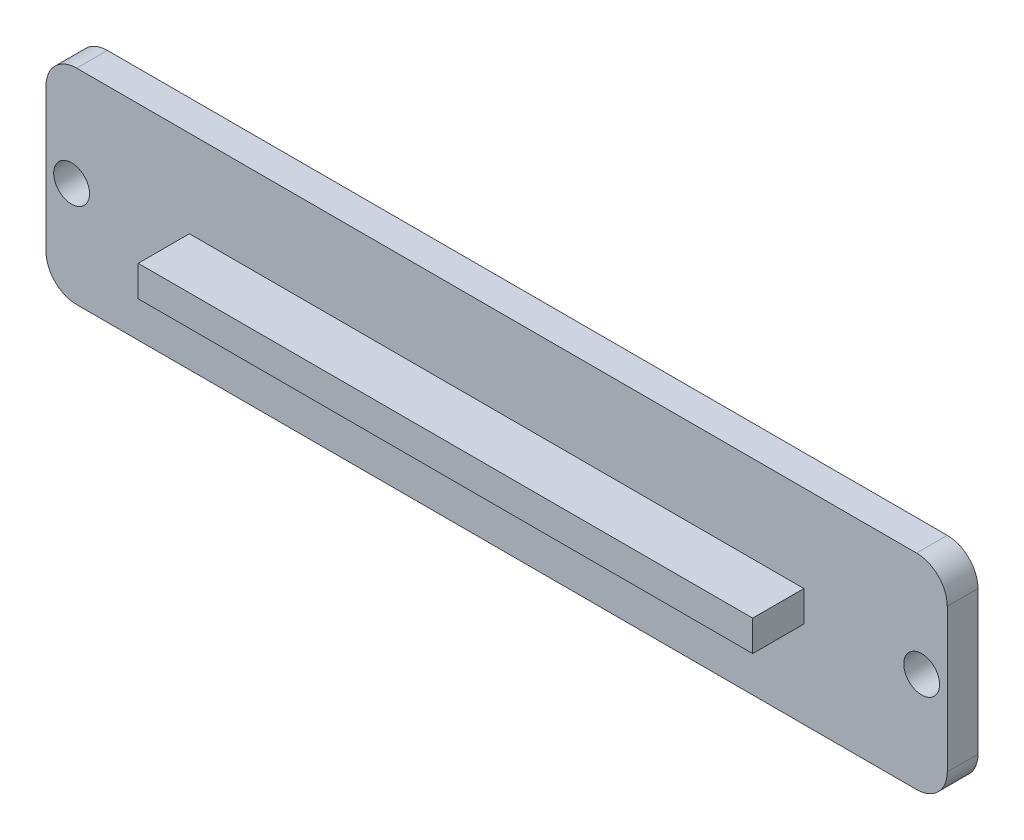
SolidWorks part; units mm, degrees
ref_plane "Plan de face" through (0, 0, 0) normal (0, 0, 1) x (1, 0, 0)
ref_plane "Plan de dessus" through (0, 0, 0) normal (0, 1, 0) x (1, 0, 0)
ref_plane "Plan de droite" through (0, 0, 0) normal (1, 0, 0) x (0, 0, -1)
sketch "Esquisse1" plane through (0, 0, 0) normal (0, 0, 1) x (1, 0, 0)
  line L0 (2.5, 10) -> (85.5, 10) construction
  line L1 (0, 0) -> (88, 0)
  line L2 (0, 0) -> (0, 20)
  line L3 (0, 20) -> (88, 20)
  line L4 (88, 0) -> (88, 20)
  circle A0 centre (2.5, 10) radius 1.75
  circle A1 centre (85.5, 10) radius 1.75
  point P9 (0, 10)
  point P10 (44, 10)
  point P11 (44, 20)
  dimension "D3" = 3.5
  dimension "D1" = 20
  dimension "D2" = 88
  dimension "D4" = 83
extrude "Boss.-Extru.1" add sketch "Esquisse1" along normal blind 3
sketch "Esquisse2" plane through (0, 0, 3) normal (0, 0, 1) x (1, 0, 0)
  line L0 (0, 20) -> (0, 0) construction
  line L1 (14, 11.5) -> (74, 11.5)
  line L2 (14, 11.5) -> (14, 8.5)
  line L3 (14, 8.5) -> (74, 8.5)
  line L4 (74, 11.5) -> (74, 8.5)
  line L5 (88, 20) -> (0, 20) construction
  point P6 (0, 10)
  point P7 (14, 10)
  point P10 (44, 20)
  point P11 (44, 11.5)
  dimension "D1" = 3
  dimension "D2" = 60
extrude "Boss.-Extru.2" add sketch "Esquisse2" along normal blind 5
fillet "Congé1" radius 3 4 edges at (88, 0, 1.5) (88, 20, 1.5) (0, 20, 1.5) (0, 0, 1.5)
